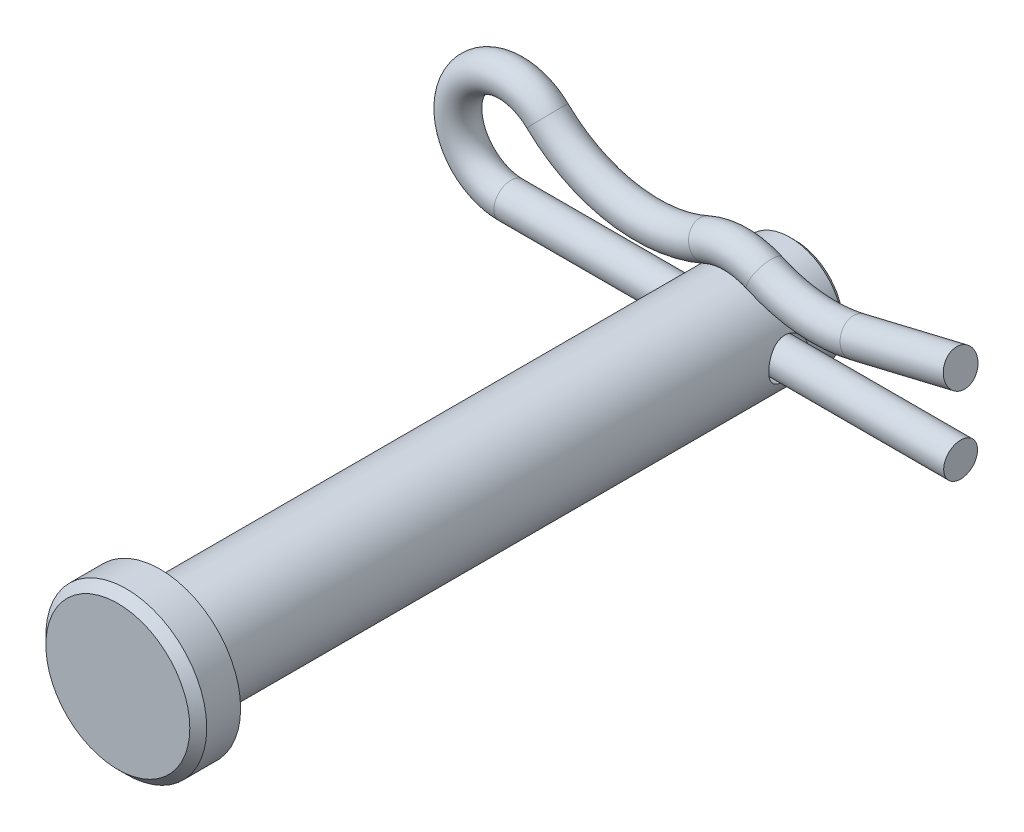
SolidWorks part; units mm, degrees
material "6061-T6 (SS)"
ref_plane "Front" through (0, 0, 0) normal (0, 0, 1) x (1, 0, 0)
ref_plane "Top" through (0, 0, 0) normal (0, 1, 0) x (1, 0, 0)
ref_plane "Right" through (0, 0, 0) normal (1, 0, 0) x (0, 0, -1)
sketch "Sketch1" plane through (0, 0, 0) normal (0, 0, 1) x (1, 0, 0)
  circle A0 centre (0, 0) radius 3.175
  point P3 (0, 3.175)
  point P4 (0, -3.175)
  dimension "dia" = 6.35
extrude "Extrude1" add sketch "Sketch1" along normal mid plane 38.1
sketch "Sketch2" plane through (0, 0, 19.05) normal (0, 0, 1) x (1, 0, 0)
  circle A0 centre (0, 0) radius 4.826
  dimension "head dia" = 9.652
extrude "Extrude2" add sketch "Sketch2" along normal blind 2.54
chamfer "Chamfer1" distance 0.508 angle 45 1 edges at (4.826, 0, 21.59)
sketch "Sketch3" plane through (0, 0, 0) normal (1, 0, 0) x (0, 0, -1)
  line L0 (-19.05, -3.175) -> (-19.05, 3.175) construction
  circle A0 centre (15.4781, 0) radius 1.1906
  point P2 (14.2875, 0)
  dimension "hole dia" = 2.3813
  dimension "useable Lg" = 33.3375
extrude "Extrude3" cut sketch "Sketch3" against normal through all and the other way through all
chamfer "Chamfer2" distance 0.3175 angle 45 1 edges at (3.175, 0, -19.05)
ref_plane "Plane1" through (0, 0, -15.4781) normal (0, 0, 1) x (1, 0, 0)
sketch "Sketch6" plane through (0, 0, -15.4781) normal (0, 0, 1) x (1, 0, 0)
  line L0 (13.4937, 0) -> (-13.4937, 0)
  line L1 (7.306, 3.2847) -> (13.4937, 4.7625)
  line L2 (-13.4937, 3.175) -> (-13.4937, 6.35) construction
  arc A0 (-13.4937, 0) -> (-11.293, 5.4635) centre (-13.4937, 3.175) cw
  arc A1 (1.7284, 3.818) -> (-1.7284, 3.818) centre (0, 0) ccw
  circle A2 centre (0, 0) radius 1.016 construction
  arc A3 (-1.7284, 3.818) -> (-11.293, 5.4635) centre (-5.2963, 11.6993) cw
  circle A4 centre (0, 4.191) radius 1.016 construction
  circle A5 centre (0, 0) radius 3.175 construction
  arc A6 (1.7284, 3.818) -> (7.306, 3.2847) centre (5.2963, 11.6993) ccw
  point P2 (-5.2963, 3.048)
  point P9 (-13.4937, 4.7625)
  point P18 (-16.6687, 3.175)
  point P22 (-13.4937, 6.35)
  point P23 (0, 1.016)
  dimension "pin dia" = 2.032
  dimension "D2" = 6.35
  dimension "pin Lg" = 30.1625
  dimension "D1" = 3.048
ref_plane "Plane2" through (13.4937, 0, -15.4781) normal (-1, 0, 0) x (0, 0, 1)
sketch "Sketch7" plane through (13.4937, 0, -15.4781) normal (-1, 0, 0) x (0, 0, 1)
  circle A0 centre (0, 0) radius 1.016
sweep "Sweep1" add profiles "Sketch7" path "Sketch6"
sketch "Sketch8" plane through (0, 0, 0) normal (1, 0, 0) x (0, 0, -1)
  line L0 (-21.59, 4.318) -> (-21.59, -4.318) construction
  line L1 (-21.082, -4.826) -> (-19.05, -4.826) construction
  line L2 (19.05, -2.8575) -> (19.05, 2.8575) construction
  line L3 (14.2875, 7.366) -> (15.4781, 7.366) construction
  line L4 (15.4781, 3.175) -> (15.4781, 6.35) construction
  arc A0 (16.4941, 6.35) -> (14.4621, 6.35) centre (15.4781, 6.35) ccw construction
  point P0 (-21.59, 4.826)
  point P1 (-19.05, 4.826)
  point P5 (19.05, 3.175)
  point P8 (-21.59, -4.826)
  point P9 (19.05, -3.175)
  point P12 (14.2875, 7.366)
equation "\"D1@Chamfer1\" = \"head ht@Extrude2\" * .2"
equation "\"D1@Chamfer2\" = \"dia@Sketch1\" * .05"
equation "\"D2@Sketch6\" = \"dia@Sketch1\" * 1"
equation "\"D1@Sketch6\" = \"pin dia@Sketch6\" * 1.5"
